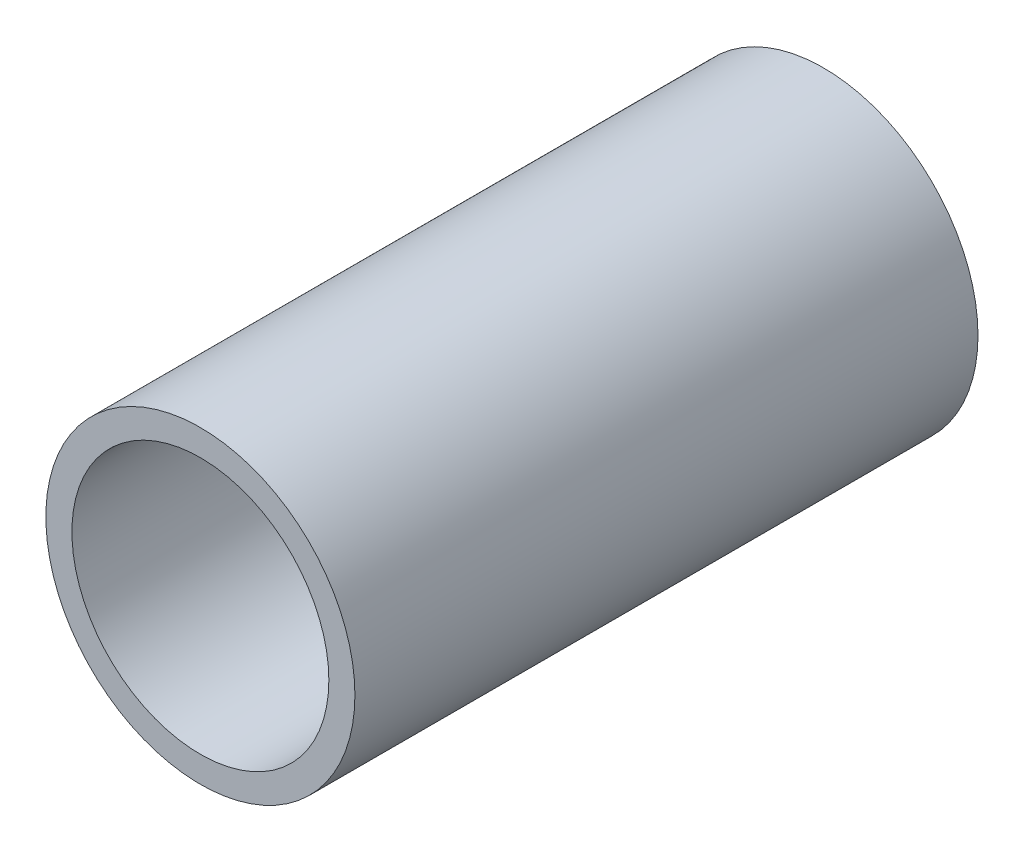
SolidWorks part; units mm, degrees
ref_plane "Front Plane" through (0, 0, 0) normal (0, 0, 1) x (1, 0, 0)
ref_plane "Top Plane" through (0, 0, 0) normal (0, 1, 0) x (1, 0, 0)
ref_plane "Right Plane" through (0, 0, 0) normal (1, 0, 0) x (0, 0, -1)
sketch "Sketch1" plane through (0, 0, 0) normal (0, 0, 1) x (1, 0, 0)
  circle A0 centre (0, 0) radius 21.082
  dimension "Pipe OD" = 42.164
extrude "Extrude-Thin1" add sketch "Sketch1" along normal mid plane 85 thin thin type one direction reverse wall 3.556
